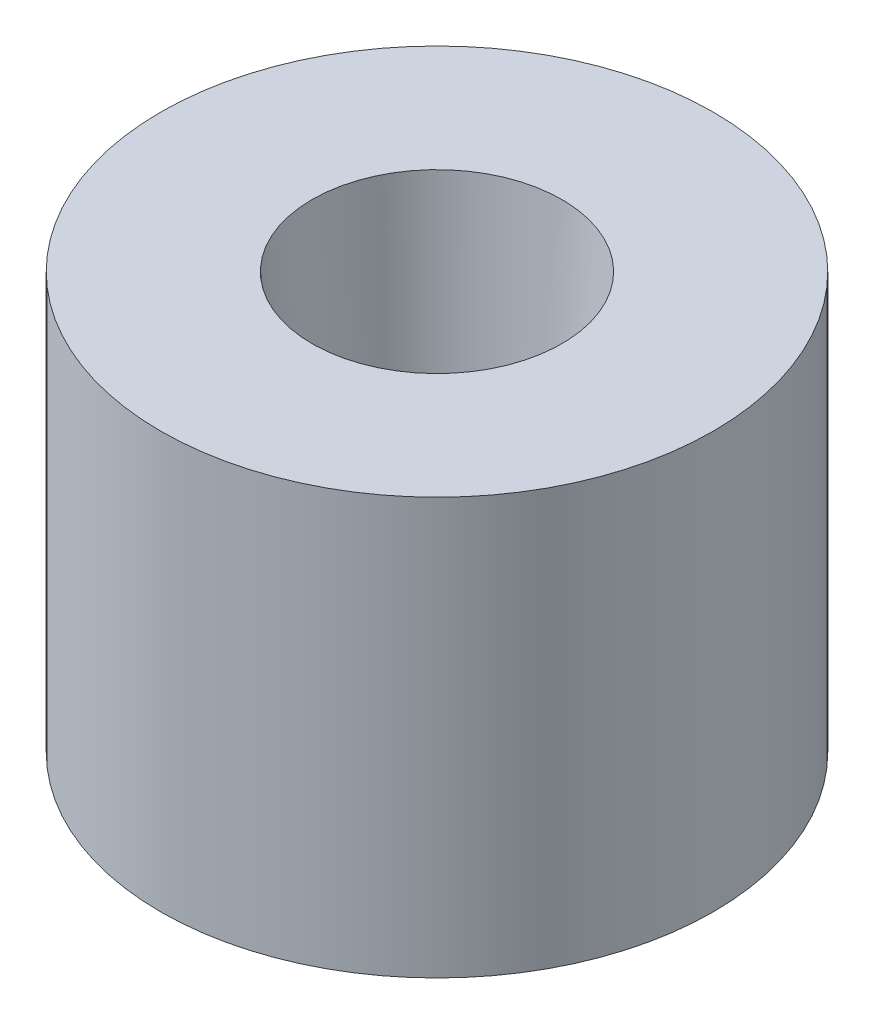
SolidWorks part; units mm, degrees
ref_plane "Front Plane" through (0, 0, 0) normal (0, 0, 1) x (1, 0, 0)
ref_plane "Top Plane" through (0, 0, 0) normal (0, 1, 0) x (1, 0, 0)
ref_plane "Right Plane" through (0, 0, 0) normal (1, 0, 0) x (0, 0, -1)
sketch "Sketch1" plane through (0, 0, 0) normal (0, 0, 1) x (1, 0, 0)
  line L0 (0, 0) -> (-3.65, 0)
  line L3 (-3.65, 0) -> (-3.65, 5.5)
  line L4 (-3.65, 5.5) -> (-1.65, 5.5)
  line L5 (-1.65, 5.5) -> (-1.43, 1.5)
  line L6 (-1.43, 1.5) -> (0, 1.5)
  line L7 (0, 1.5) -> (0, 0)
  dimension "D1" = 1.43
  dimension "D2" = 1.65
  dimension "D3" = 1.5
  dimension "D4" = 2
  dimension "D5" = 4
revolve "Revolve1" add sketch "Sketch1" angle 360 about L7
